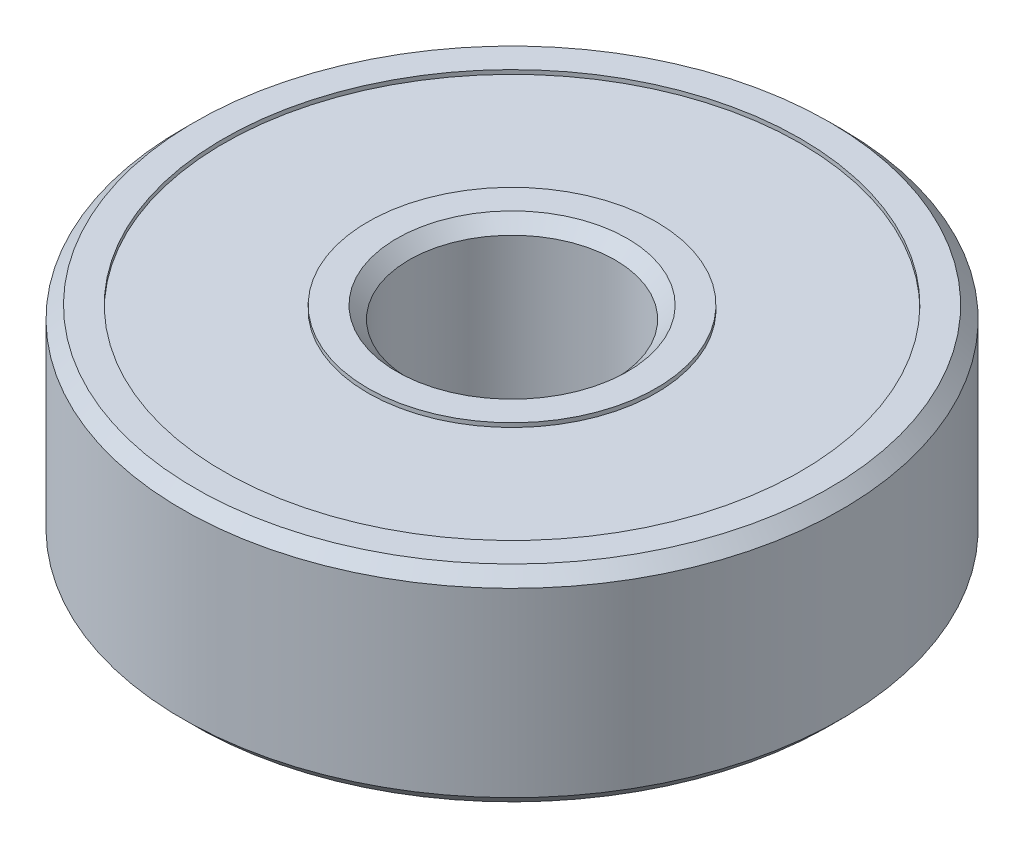
SolidWorks part; units mm, degrees
ref_plane "Plane1" through (0, 0, 0) normal (0, 0, 1) x (1, 0, 0)
ref_plane "Plane2" through (0, 0, 0) normal (0, 1, 0) x (1, 0, 0)
ref_plane "Plane3" through (0, 0, 0) normal (1, 0, 0) x (0, 0, -1)
sketch "Sketch1" plane through (0, 0, 0) normal (0, 0, 1) x (1, 0, 0)
  line L0 (0, 0) -> (0, 31.1803) construction
  line L1 (2.5, -2.2) -> (2.5, 2.2)
  line L2 (2.8, 2.5) -> (3.5, 2.5)
  line L3 (3.5, 2.5) -> (3.5, 2.4)
  line L4 (3.5, 2.4) -> (7, 2.4)
  line L5 (7, 2.4) -> (7, 2.5)
  line L6 (7, 2.5) -> (7.7, 2.5)
  line L7 (8, 2.2) -> (8, -2.2)
  line L8 (0, 0) -> (8, 0) construction
  line L9 (2.5, 2.2) -> (2.8, 2.5)
  line L10 (7.7, 2.5) -> (8, 2.2)
  line L11 (7.7, -2.5) -> (8, -2.2)
  line L12 (7, -2.5) -> (7.7, -2.5)
  line L13 (7, -2.4) -> (7, -2.5)
  line L14 (3.5, -2.4) -> (7, -2.4)
  line L15 (3.5, -2.5) -> (3.5, -2.4)
  line L16 (2.8, -2.5) -> (3.5, -2.5)
  line L17 (2.5, -2.2) -> (2.8, -2.5)
  point P4 (2.5, 2.5)
  point P10 (8, 2.5)
  point P23 (2.5, 0)
  dimension "D1" = 0.1
  dimension "D2" = 5
  dimension "D3" = 5
  dimension "D4" = 1
  dimension "D5" = 1
  dimension "D6" = 16
revolve "Revolution1" add sketch "Sketch1" angle 360 about L0
